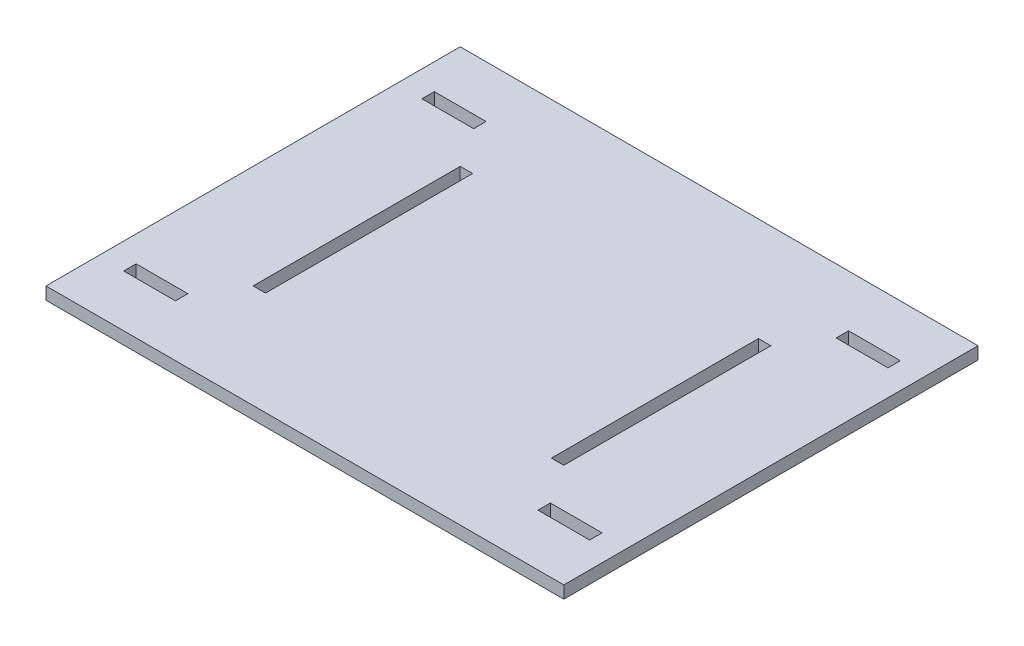
SolidWorks part; units mm, degrees
ref_plane "Front Plane" through (0, 0, 0) normal (0, 0, 1) x (1, 0, 0)
ref_plane "Top Plane" through (0, 0, 0) normal (0, 1, 0) x (1, 0, 0)
ref_plane "Right Plane" through (0, 0, 0) normal (1, 0, 0) x (0, 0, -1)
sketch "Sketch1" plane through (0, 0, 0) normal (0, 1, 0) x (1, 0, 0)
  line L1 (-250, 200) -> (250, 200)
  line L2 (-250, 200) -> (-250, -200)
  line L3 (-250, -200) -> (250, -200)
  line L4 (250, 200) -> (250, -200)
  line L5 (-250, 200) -> (250, -200) construction
  line L6 (-250, -200) -> (250, 200) construction
  point P0 (0, 0)
  dimension "D1" = 500
  dimension "D2" = 400
extrude "Boss-Extrude1" add sketch "Sketch1" along normal blind 12 contours L2 L3 L4 L1
sketch "Sketch2" plane through (0, 12, 0) normal (0, 1, 0) x (1, 0, 0)
  line L0 (-6.6, 0) -> (6.6, 0) construction
  line L1 (-150, 100) -> (-138, 100)
  line L2 (-150, 100) -> (-150, -100)
  line L3 (-150, -100) -> (-138, -100)
  line L4 (-138, 100) -> (-138, -100)
  line L5 (-150, 100) -> (-138, -100) construction
  line L6 (-150, -100) -> (-138, 100) construction
  line L20 (-250, 200) -> (-250, -200) construction
  point P0 (-144, 0)
  dimension "D1" = 200
  dimension "D2" = 12
  dimension "D7" = 100
extrude "Cut-Extrude1" cut sketch "Sketch2" against normal up to surface (12 mm away) contours L4 L3 L2 L1 up to face at (0, 0, 0)
mirror "Mirror2" about plane through (0, 0, 0) normal (1, 0, 0) of "Cut-Extrude1"
sketch "Sketch5" plane through (0, 12, 0) normal (0, 1, 0) x (1, 0, 0)
  line L0 (-150, 100) -> (-150, -100) construction
  line L1 (-225, 150) -> (-175, 150)
  line L2 (-225, 150) -> (-225, 138)
  line L3 (-225, 138) -> (-175, 138)
  line L4 (-175, 150) -> (-175, 138)
  line L5 (-225, 150) -> (-175, 138) construction
  line L6 (-225, 138) -> (-175, 150) construction
  line L7 (-250, 200) -> (250, 200) construction
  point P0 (-200, 144)
  dimension "D1" = 12
  dimension "D2" = 50
  dimension "D3" = 25
  dimension "D4" = 50
extrude "Cut-Extrude2" cut sketch "Sketch5" against normal up to surface (12 mm away) up to face at (144, 0, 0)
mirror "Mirror5" about plane through (0, 0, 0) normal (0, 0, 1) of "Cut-Extrude2" second plane through (0, 0, 0) second plane normal (1, 0, 0)
